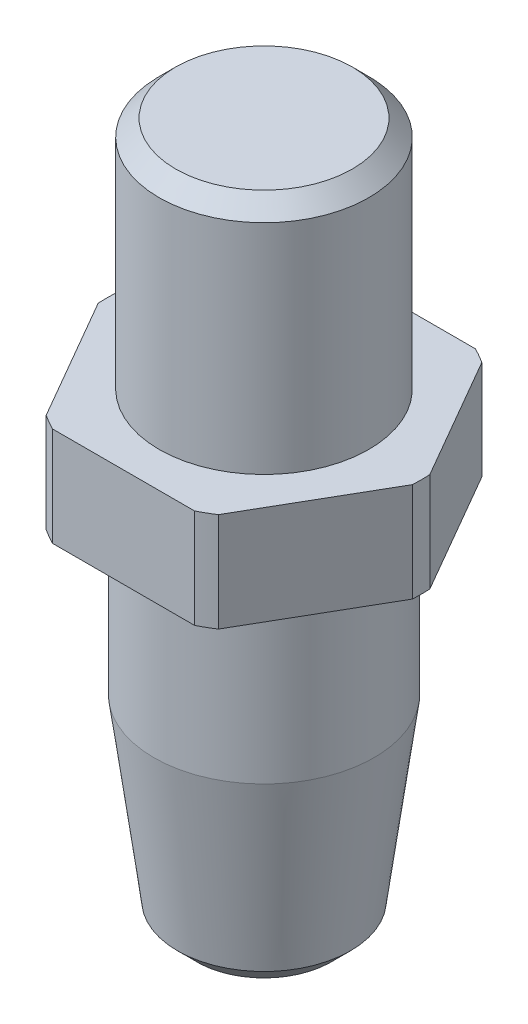
SolidWorks part; units mm, degrees
material "AISI 4340 Steel, normalized"
ref_plane "Front Plane" through (0, 0, 0) normal (0, 0, 1) x (1, 0, 0)
ref_plane "Top Plane" through (0, 0, 0) normal (0, 1, 0) x (1, 0, 0)
ref_plane "Right Plane" through (0, 0, 0) normal (1, 0, 0) x (0, 0, -1)
sketch "Sketch1" plane through (0, 0, 0) normal (0, 0, 1) x (1, 0, 0)
  line L0 (-6.6675, 0) -> (-9.525, 0)
  line L1 (-9.525, 0) -> (-9.525, 6)
  line L2 (-9.525, 6) -> (-6.35, 6)
  line L3 (-6.35, 6) -> (-6.35, 20.2)
  line L4 (0, 72.0465) -> (0, -75.2102) construction
  line L5 (-6.35, 20.2) -> (0, 20.2)
  line L6 (-6.6675, 0) -> (-6.6675, -10)
  line L7 (-6.6675, -22) -> (-5.08, -22) construction
  line L8 (0, 20.2) -> (0, -22)
  line L9 (-6.6675, -10) -> (-5.08, -22)
  line L10 (-6.6675, -10) -> (-6.6675, -22) construction
  line L11 (-5.08, -22) -> (0, -22)
  dimension "D1" = 19.05
  dimension "D2" = 6
  dimension "D3" = 13.335
  dimension "D4" = 14.2
  dimension "D5" = 10
  dimension "D6" = 12.7
  dimension "D7" = 10.16
  dimension "D8" = 12
  dimension "D9" = 42.2
revolve "Revolve1" add sketch "Sketch1" angle 360 about L4
cosmetic thread "Cosmetic Thread1" parameters "D1"=9, "D2"=11.1887
chamfer "Chamfer1" distance 1 angle 45 2 edges at (0, 20.2, 6.35) (0, -22, 5.08)
sketch "Sketch2" plane through (0, 0, 0) normal (0, 0, 1) x (1, 0, 0)
  line L0 (0, -14.5914) -> (0, 22.8649) construction
fillet "Fillet1" [suppressed] radius 0.5
sketch "Sketch3" plane through (0, 0, 0) normal (1, 0, 0) x (0, 0, -1)
  line L0 (-6.6675, -10) -> (6.6675, -10) construction
  line L1 (-5.5118, -10) -> (-10.8903, -10)
  line L2 (-5.5118, -10) -> (-5.5118, -21.5593)
  line L3 (-5.5118, -21.5593) -> (-10.8903, -21.5593)
  line L4 (-10.8903, -10) -> (-10.8903, -21.5593)
  line L5 (0, 0) -> (0, -23.7447) construction
  line L6 (10.8903, -10) -> (10.8903, -21.5593)
  line L7 (5.5118, -21.5593) -> (10.8903, -21.5593)
  line L8 (5.5118, -10) -> (5.5118, -21.5593)
  line L9 (5.5118, -10) -> (10.8903, -10)
  dimension "D1" = 11.0236
extrude "Cut-Extrude1" [suppressed] cut sketch "Sketch3" against normal through all and the other way through all
sketch "Sketch4" plane through (0, 0, 0) normal (0, 1, 0) x (1, 0, 0)
  line L1 (9.815, 0) -> (4.9075, 8.5)
  line L2 (4.9075, 8.5) -> (-4.9075, 8.5)
  line L3 (-4.9075, 8.5) -> (-9.815, 0)
  line L4 (-9.815, 0) -> (-4.9075, -8.5)
  line L5 (-4.9075, -8.5) -> (4.9075, -8.5)
  line L6 (4.9075, -8.5) -> (9.815, 0)
  circle A0 centre (0, 0) radius 8.5 construction
  dimension "D1" = 17
extrude "Cut-Extrude3" cut sketch "Sketch4" along normal through all flip side to cut
move or copy body "Body-Move/Copy1" [suppressed] bodies to move or copy 101
